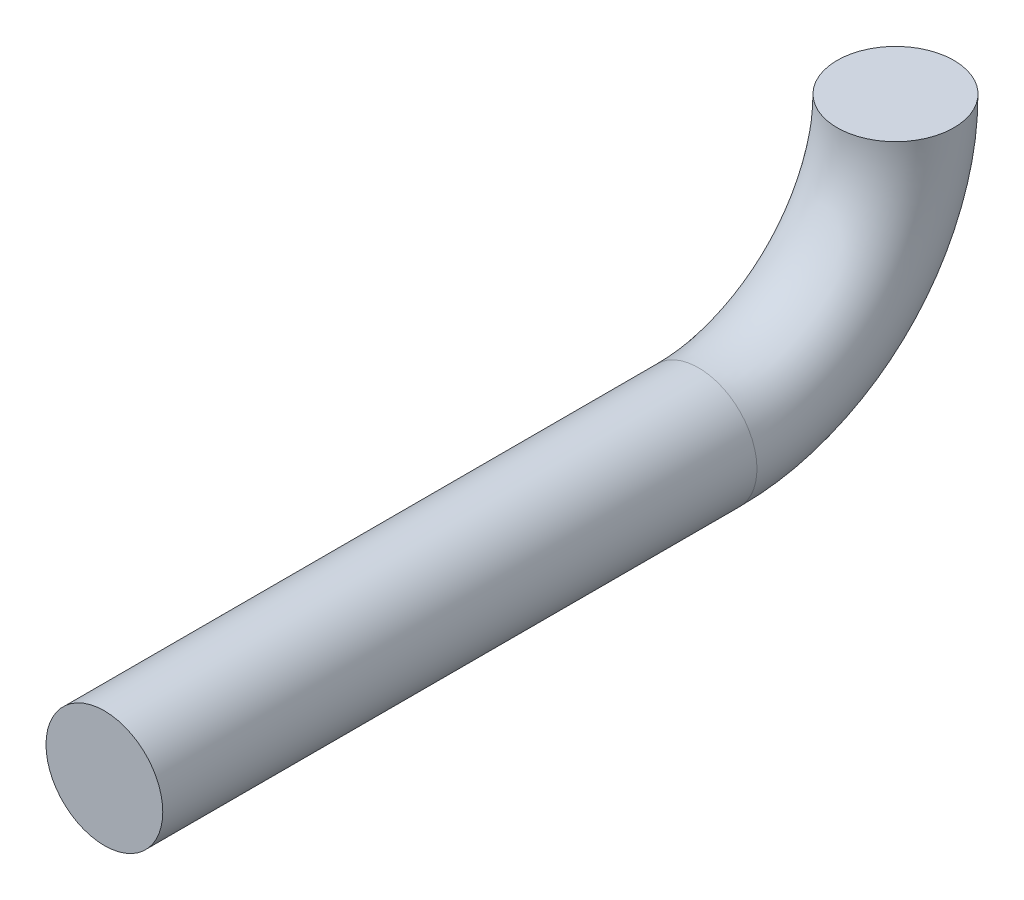
SolidWorks part; units mm, degrees
ref_plane "Front Plane" through (0, 0, 0) normal (0, 0, 1) x (1, 0, 0)
ref_plane "Top Plane" through (0, 0, 0) normal (0, 1, 0) x (1, 0, 0)
ref_plane "Right Plane" through (0, 0, 0) normal (1, 0, 0) x (0, 0, -1)
sketch "Sketch1" plane through (0, 0, 0) normal (1, 0, 0) x (0, 0, -1)
  line L0 (0, -0.8568) -> (-2.585, -0.8568)
  arc A0 (0, -0.8568) -> (0.8568, 0) centre (0, 0) ccw
sketch "Sketch2" plane through (0, 0, 0) normal (0, 1, 0) x (1, 0, 0)
  circle A0 centre (0, 0.8568) radius 0.254
  point P2 (0, 0.8568)
sweep "Sweep1" add profiles "Sketch2" path "Sketch1"
